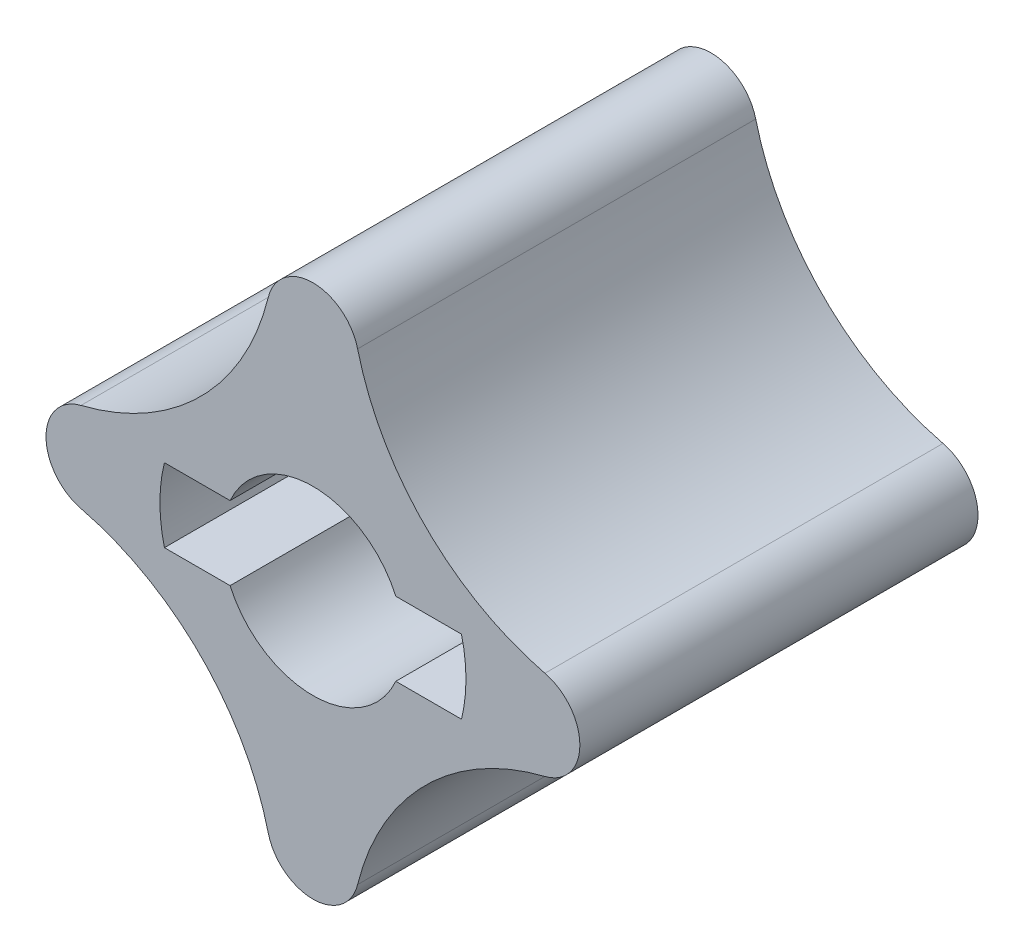
SolidWorks part; units mm, degrees
material "6063-T6"
ref_plane "Plane1" through (0, 0, 0) normal (0, 0, 1) x (1, 0, 0)
ref_plane "Plane2" through (0, 0, 0) normal (0, 1, 0) x (-1, 0, 0)
ref_plane "Plane3" through (0, 0, 0) normal (1, 0, 0) x (0, 0, -1)
sketch "Sketch1" plane through (0, 0, 0) normal (0, 0, 1) x (1, 0, 0)
  line L0 (0, 12.192) -> (0, -12.192) construction
  line L1 (-12.192, 0) -> (12.192, 0) construction
  line L8 (50, 0) -> (-50, 0) construction
  arc A2 (2.4657, 12.802) -> (-2.4657, 12.802) centre (0, 12.192) ccw
  arc A3 (12.802, -2.4657) -> (12.802, 2.4657) centre (12.192, 0) ccw
  arc A4 (-2.4657, -12.802) -> (2.4657, -12.802) centre (0, -12.192) ccw
  arc A5 (-12.802, 2.4657) -> (-12.802, -2.4657) centre (-12.192, 0) ccw
  arc A6 (2.4657, 12.802) -> (12.802, 2.4657) centre (16.1995, 16.1995) ccw
  arc A8 (-12.802, -2.4657) -> (-2.4657, -12.802) centre (-16.1995, -16.1995) cw
  arc A9 (-2.4657, 12.802) -> (-12.802, 2.4657) centre (-16.1995, 16.1995) cw
  arc A10 (12.802, -2.4657) -> (2.4657, -12.802) centre (16.1995, -16.1995) ccw
  circle A11 centre (0, 0) radius 5.0038
  dimension "D1" = 14.1478
  dimension "D2" = 5.08
  dimension "D3" = 24.384
  dimension "D4" = 10.0076
extrude "Base-Extrude" add sketch "Sketch1" along normal blind 21.971
sketch "Sketch2" plane through (0, 0, 21.971) normal (0, 0, 1) x (1, 0, 0)
  line L0 (-8.1974, 2.032) -> (8.1974, 2.032)
  line L1 (-8.1974, -2.032) -> (8.1974, -2.032)
  arc A0 (-8.1974, 2.032) -> (-8.1974, -2.032) centre (0, 0) ccw
  arc A2 (8.1974, -2.032) -> (8.1974, 2.032) centre (0, 0) ccw
  circle A3 centre (0, 0) radius 5.0038 construction
  dimension "D1" = 16.891
  dimension "D2" = 4.064
extrude "Cut-Extrude1" cut sketch "Sketch2" against normal blind 15.113
